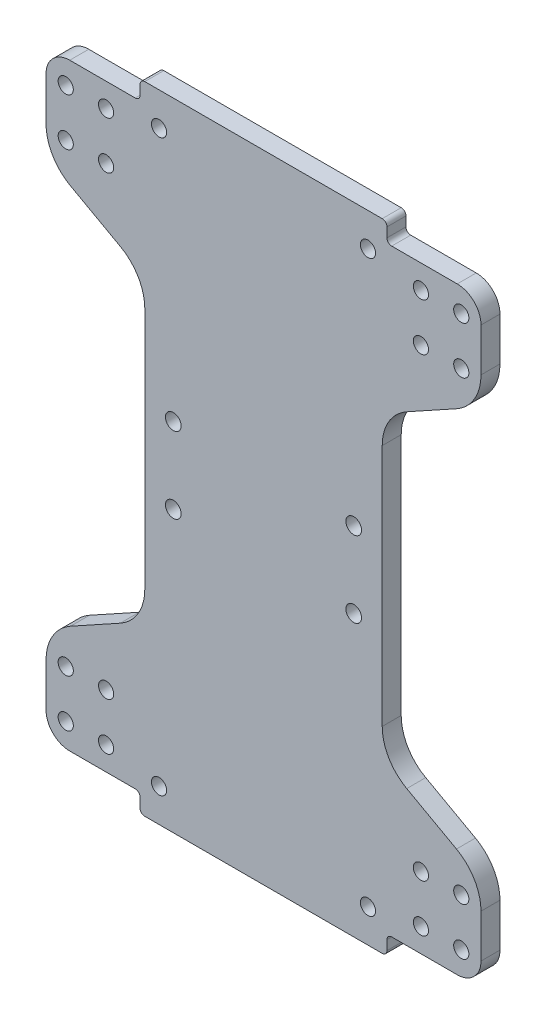
SolidWorks part; units mm, degrees
material "Acrylic (Medium-high impact)"
ref_plane "Front Plane" through (0, 0, 0) normal (0, 0, 1) x (1, 0, 0)
ref_plane "Top Plane" through (0, 0, 0) normal (0, 1, 0) x (1, 0, 0)
ref_plane "Right Plane" through (0, 0, 0) normal (1, 0, 0) x (0, 0, -1)
sketch "Sketch1" plane through (0, 0, 0) normal (0, 0, 1) x (1, 0, 0)
  line L0 (1.25, 62.9364) -> (93.1655, 62.9364) construction
  line L1 (1.4077, -0.0636) -> (20.2069, -0.0636)
  line L2 (1.4077, -0.0636) -> (1.4077, 19.9364)
  line L3 (69.2085, 2.9364) -> (69.2085, -10.0636) construction
  line L4 (80.3577, 4.9364) -> (80.3577, 14.9364) construction
  line L5 (1.4077, 19.9364) -> (22.2077, 31.43)
  line L6 (25.2069, 2.9364) -> (47.2077, 2.9364) construction
  line L7 (88.8577, 14.9364) -> (80.3577, 14.9364) construction
  line L8 (47.2077, -14.0636) -> (47.2077, 139.9364) construction
  line L9 (88.8577, 4.9364) -> (88.8577, 14.9364) construction
  line L10 (21.2069, -1.0636) -> (21.2069, -3.0636)
  line L11 (22.2077, 94.4428) -> (22.2077, 31.43)
  line L12 (88.8577, 4.9364) -> (80.3577, 4.9364) construction
  line L13 (80.3577, 9.9364) -> (88.8577, 9.9364) construction
  line L14 (14.0577, 9.9364) -> (5.5577, 9.9364) construction
  line L15 (5.5577, 4.9364) -> (14.0577, 4.9364) construction
  line L16 (5.5577, 4.9364) -> (5.5577, 14.9364) construction
  line L17 (5.5577, 14.9364) -> (14.0577, 14.9364) construction
  line L18 (14.0577, 4.9364) -> (14.0577, 14.9364) construction
  line L19 (72.2077, 94.4428) -> (72.2077, 31.43)
  line L20 (73.2085, -1.0636) -> (73.2085, -3.0636)
  line L21 (93.0077, 19.9364) -> (72.2077, 31.43)
  line L22 (93.0077, -0.0636) -> (93.0077, 19.9364)
  line L23 (93.0077, -0.0636) -> (74.2085, -0.0636)
  line L24 (25.2069, 122.9364) -> (25.2069, 135.9364) construction
  line L25 (14.0577, 120.9364) -> (14.0577, 110.9364) construction
  line L26 (5.5577, 110.9364) -> (14.0577, 110.9364) construction
  line L27 (5.5577, 120.9364) -> (5.5577, 110.9364) construction
  line L28 (5.5577, 120.9364) -> (14.0577, 120.9364) construction
  line L29 (14.0577, 115.9364) -> (5.5577, 115.9364) construction
  line L30 (80.3577, 115.9364) -> (88.8577, 115.9364) construction
  line L31 (88.8577, 120.9364) -> (80.3577, 120.9364) construction
  line L32 (88.8577, 120.9364) -> (88.8577, 110.9364) construction
  line L33 (88.8577, 110.9364) -> (80.3577, 110.9364) construction
  line L34 (25.2069, 122.9364) -> (47.2077, 122.9364) construction
  line L35 (22.2069, 129.9364) -> (72.2085, 129.9364)
  line L36 (80.3577, 120.9364) -> (80.3577, 110.9364) construction
  line L37 (69.2085, 122.9364) -> (69.2085, 135.9364) construction
  line L38 (25.2069, 2.9364) -> (25.2069, -10.0636) construction
  line L39 (73.2085, 126.9364) -> (73.2085, 128.9364)
  line L40 (93.0077, 125.9364) -> (74.2085, 125.9364)
  line L41 (93.0077, 125.9364) -> (93.0077, 105.9364)
  line L42 (93.0077, 105.9364) -> (72.2077, 94.4428)
  line L43 (21.2069, 126.9364) -> (21.2069, 128.9364)
  line L45 (1.4077, 105.9364) -> (22.2077, 94.4428)
  line L46 (1.4077, 125.9364) -> (1.4077, 105.9364)
  line L47 (1.4077, 125.9364) -> (20.2069, 125.9364)
  line L48 (22.2069, -4.0636) -> (72.2085, -4.0636)
  circle A0 centre (5.5577, 4.9364) radius 1.6
  circle A1 centre (14.0577, 4.9364) radius 1.6
  circle A2 centre (14.0577, 14.9364) radius 1.6
  circle A3 centre (5.5577, 14.9364) radius 1.6
  arc A4 (72.2085, -4.0636) -> (73.2085, -3.0636) centre (72.2085, -3.0636) ccw
  arc A5 (73.2085, -1.0636) -> (74.2085, -0.0636) centre (74.2085, -1.0636) cw
  arc A6 (22.2069, -4.0636) -> (21.2069, -3.0636) centre (22.2069, -3.0636) cw
  circle A7 centre (69.2085, 2.9364) radius 1.6
  circle A9 centre (66.2077, 54.9364) radius 1.65
  circle A10 centre (88.8577, 14.9364) radius 1.6
  circle A11 centre (80.3577, 14.9364) radius 1.6
  circle A12 centre (80.3577, 4.9364) radius 1.6
  circle A13 centre (88.8577, 4.9364) radius 1.6
  arc A14 (22.2069, 129.9364) -> (21.2069, 128.9364) centre (22.2069, 128.9364) ccw
  arc A15 (21.2069, 126.9364) -> (20.2069, 125.9364) centre (20.2069, 126.9364) cw
  circle A16 centre (28.2077, 54.9364) radius 1.65
  arc A17 (72.2085, 129.9364) -> (73.2085, 128.9364) centre (72.2085, 128.9364) cw
  circle A18 centre (25.2069, 2.9364) radius 1.6
  circle A19 centre (25.2069, 122.9364) radius 1.6
  circle A20 centre (28.2077, 70.9364) radius 1.65
  circle A22 centre (88.8577, 120.9364) radius 1.6
  arc A23 (21.2069, -1.0636) -> (20.2069, -0.0636) centre (20.2069, -1.0636) ccw
  circle A25 centre (80.3577, 120.9364) radius 1.6
  circle A26 centre (80.3577, 110.9364) radius 1.6
  circle A27 centre (88.8577, 110.9364) radius 1.6
  circle A28 centre (66.2077, 70.9364) radius 1.65
  circle A30 centre (69.2085, 122.9364) radius 1.6
  arc A32 (73.2085, 126.9364) -> (74.2085, 125.9364) centre (74.2085, 126.9364) ccw
  circle A34 centre (5.5577, 110.9364) radius 1.6
  circle A35 centre (14.0577, 110.9364) radius 1.6
  circle A36 centre (14.0577, 120.9364) radius 1.6
  circle A37 centre (5.5577, 120.9364) radius 1.6
  point P61 (47.2077, 62.9364)
  point P108 (72.2077, 62.9364)
  point P109 (22.2077, 62.9364)
  dimension "D10" = 3.2
  dimension "D5" = 45.8
  dimension "D32" = 1
  dimension "D17" = 1
  dimension "D1" = 63
  dimension "D2" = 19
  dimension "D3" = 20
  dimension "D4" = 8
  dimension "D6" = 10
  dimension "D7" = 8.5
  dimension "D8" = 53
  dimension "D9" = 4.15
  dimension "D11" = 13
  dimension "D12" = 7
  dimension "D14" = 25
  dimension "D16" = 4
extrude "Boss-Extrude1" add sketch "Sketch1" along normal blind 4
fillet "Fillet2" radius 10 8 edges at (1.4077, 19.9364, 2) (22.2077, 31.43, 2) (93.0077, 19.9364, 2) (72.2077, 31.43, 2) (93.0077, 105.9364, 2) (72.2077, 94.4428, 2) (1.4077, 105.9364, 2) (22.2077, 94.4428, 2)
fillet "Fillet3" radius 5 4 edges at (1.4077, -0.0636, 2) (1.4077, 125.9364, 2) (93.0077, 125.9364, 2) (93.0077, -0.0636, 2)
